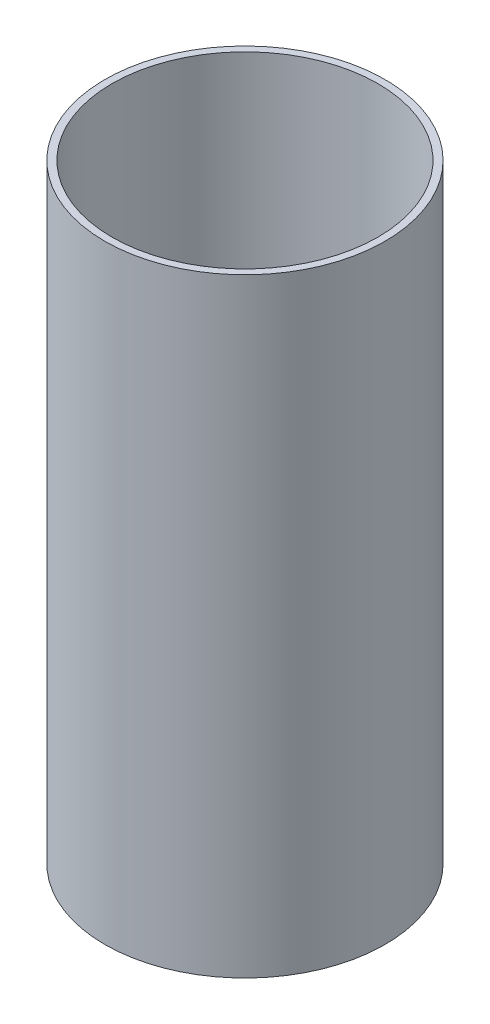
SolidWorks part; units mm, degrees
material "PVC Rigid"
ref_plane "Front Plane" through (0, 0, 0) normal (0, 0, 1) x (1, 0, 0)
ref_plane "Top Plane" through (0, 0, 0) normal (0, 1, 0) x (1, 0, 0)
ref_plane "Right Plane" through (0, 0, 0) normal (1, 0, 0) x (0, 0, -1)
sketch "Sketch1" plane through (0, 0, 0) normal (0, 1, 0) x (1, 0, 0)
  circle A0 centre (0, 0) radius 93.6625
  circle A1 centre (0, 0) radius 88.9
  dimension "D1" = 187.325
  dimension "D2" = 177.8
extrude "Boss-Extrude1" add sketch "Sketch1" along normal mid plane 407.162
